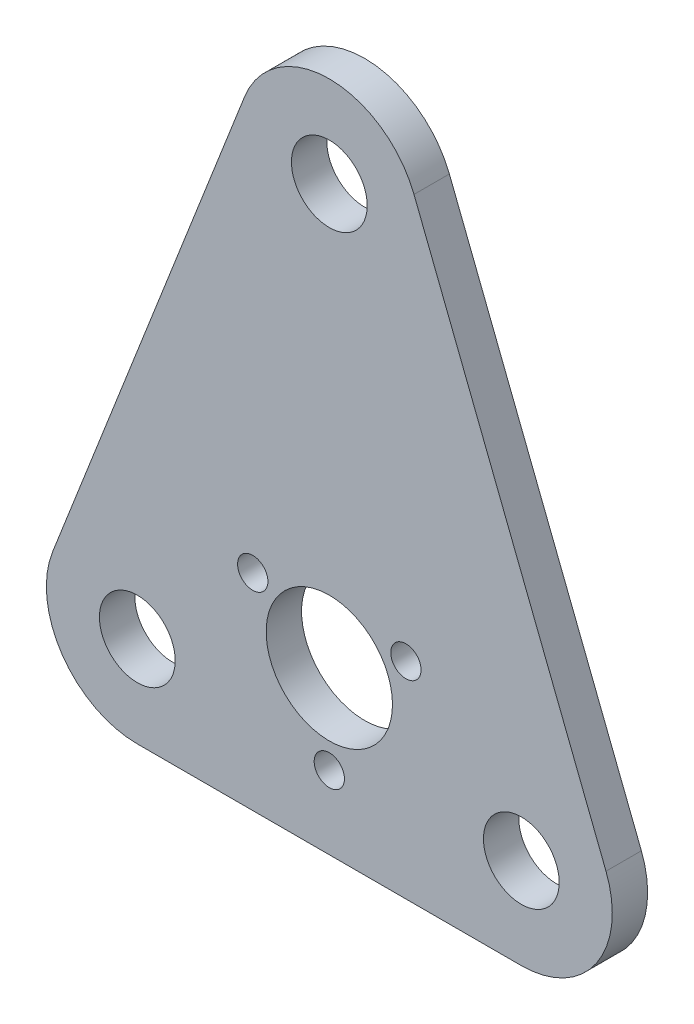
SolidWorks part; units mm, degrees
material "Plain Carbon Steel"
ref_plane "Front Plane" through (0, 0, 0) normal (0, 0, 1) x (1, 0, 0)
ref_plane "Top Plane" through (0, 0, 0) normal (0, 1, 0) x (1, 0, 0)
ref_plane "Right Plane" through (0, 0, 0) normal (1, 0, 0) x (0, 0, -1)
sketch "Sketch1" plane through (0, 0, 0) normal (0, 0, 1) x (1, 0, 0)
  line L0 (0, 0) -> (0, 97) construction
  line L1 (-38, 0) -> (38, 0) construction
  line L2 (-54.7598, 6.5657) -> (-16.7598, 103.5657)
  line L3 (54.7598, 6.5657) -> (16.7598, 103.5657)
  line L4 (-38, -18) -> (38, -18)
  line L5 (0, 14) -> (-19.4967, 25.2564) construction
  arc A0 (16.7598, 103.5657) -> (-16.7598, 103.5657) centre (0, 97) ccw
  arc A1 (-54.7598, 6.5657) -> (-38, -18) centre (-38, 0) ccw
  arc A2 (38, -18) -> (54.7598, 6.5657) centre (38, 0) ccw
  circle A4 centre (0, 97) radius 7.5
  circle A5 centre (-38, 0) radius 7.5
  circle A6 centre (38, 0) radius 7.5
  circle A7 centre (0, 14) radius 12.5
  circle A8 centre (0, 14) radius 17.5 construction
  circle A9 centre (0, -3.5) radius 3
  circle A10 centre (-15.1554, 22.75) radius 3
  circle A11 centre (15.1554, 22.75) radius 3
  point P29 (0, 14)
  dimension "D1" = 36
  dimension "D4" = 97
  dimension "D5" = 15
  dimension "D6" = 25
  dimension "D7" = 35
  dimension "D8" = 6
  dimension "D2" = 76
  dimension "D3" = 32
  dimension "D10" = 30
  dimension "D9" = 3
extrude "Boss-Extrude1" add sketch "Sketch1" along normal blind 7
